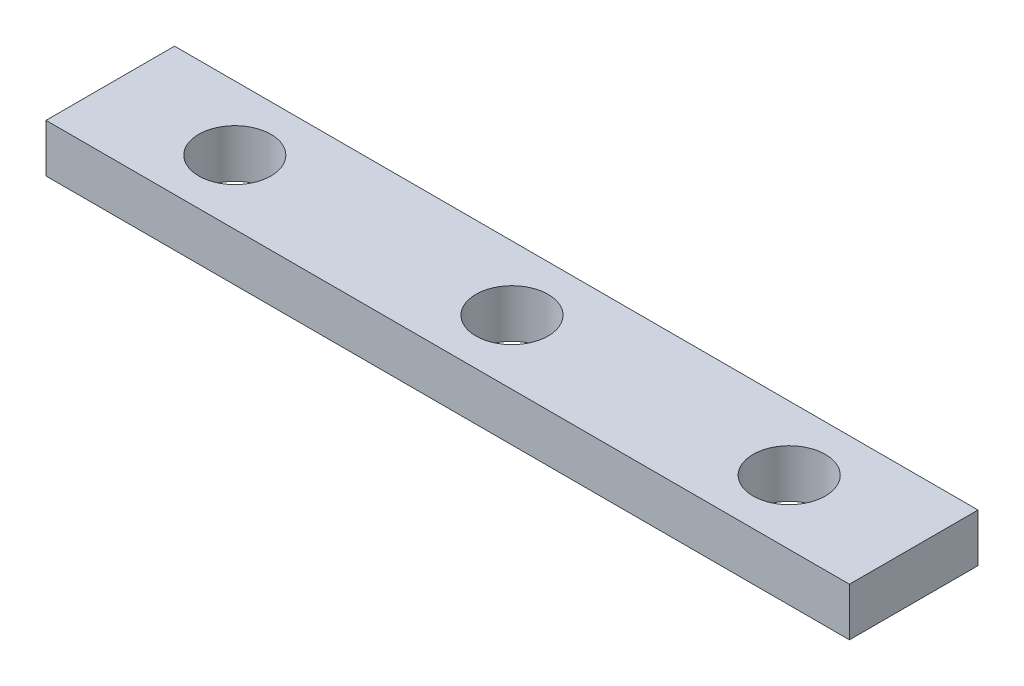
SolidWorks part; units mm, degrees
ref_plane "Front Plane" through (0, 0, 0) normal (0, 0, 1) x (1, 0, 0)
ref_plane "Top Plane" through (0, 0, 0) normal (0, 1, 0) x (1, 0, 0)
ref_plane "Right Plane" through (0, 0, 0) normal (1, 0, 0) x (0, 0, -1)
sketch "Sketch1" plane through (0, 0, 0) normal (0, 1, 0) x (1, 0, 0)
  line L1 (-7.2264, 4.3136) -> (42.7736, 4.3136)
  line L2 (-7.2264, 4.3136) -> (-7.2264, -3.6864)
  line L3 (-7.2264, -3.6864) -> (42.7736, -3.6864)
  line L4 (42.7736, 4.3136) -> (42.7736, -3.6864)
  dimension "D1" = 8
  dimension "D2" = 50
extrude "Boss-Extrude1" add sketch "Sketch1" along normal blind 3
hole_wizard "#8 Clearance Hole1" positions "3DSketch1" profile "Sketch2" hole size "#8" standard "ANSI Inch"
sketch3d "3DSketch1"
  line L0 (-7.2264, 3, -4.3136) -> (-7.2264, 3, 3.6864) construction
  line L1 (42.7736, 3, 3.6864) -> (42.7736, 3, -4.3136) construction
  line L2 (-7.2264, 3, 3.6864) -> (42.7736, 3, 3.6864) construction
  point P0 (0.5236, 3, -0.3136)
  point P2 (35.0236, 3, -0.3136)
  point P12 (17.7736, 3, -0.3136)
  dimension "D1" = 7.75
  dimension "D2" = 7.75
  dimension "D3" = 4
  dimension "D4" = 4
  dimension "D5" = 4
  dimension "D6" = 25
  dimension "D7" = 34.5
sketch "Sketch2" plane through (0.5236, 3, -0.3136) normal (1, 0, 0) x (0, 0, 1)
  line L0 (0, 0) -> (0, 18.3507)
  line L1 (0, 18.3507) -> (2.2479, 17)
  line L2 (2.2479, 17) -> (2.2479, 0)
  line L5 (2.2479, 0) -> (0, 0)
  line L10 (0, 18.3507) -> (-2.2479, 17) construction
  line L11 (0, -6.35) -> (0, 107.95) construction
  dimension "Hole Dia." = 4.4958
  dimension "Hole Depth" = 17
  dimension "Drill Angle" = 118
